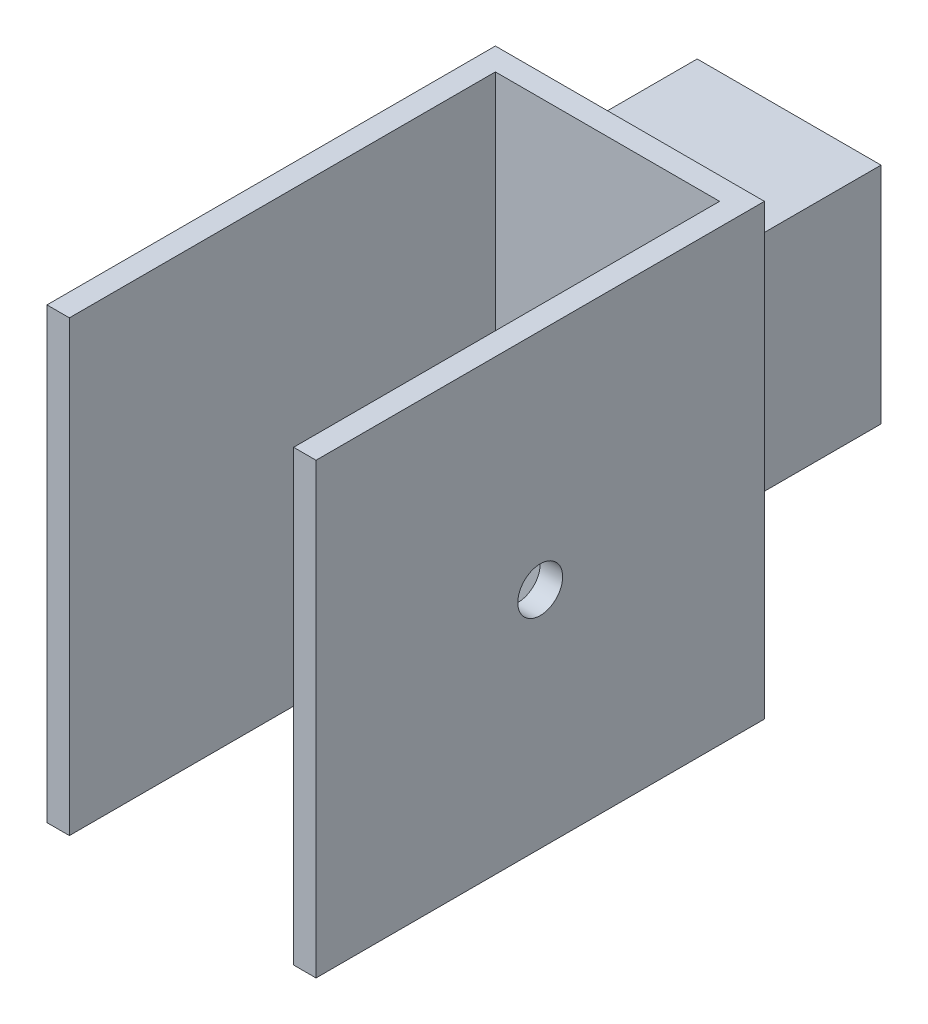
SolidWorks part; units mm, degrees
ref_plane "Piano frontale" through (0, 0, 0) normal (0, 0, 1) x (1, 0, 0)
ref_plane "Piano superiore" through (0, 0, 0) normal (0, 1, 0) x (1, 0, 0)
ref_plane "Piano destro" through (0, 0, 0) normal (1, 0, 0) x (0, 0, -1)
sketch "Schizzo1" plane through (0, 0, 0) normal (0, 0, 1) x (1, 0, 0)
  line L1 (30, -50) -> (-30, -50)
  line L2 (30, -50) -> (30, 50)
  line L3 (30, 50) -> (-30, 50)
  line L4 (-30, -50) -> (-30, 50)
  line L5 (30, -50) -> (-30, 50) construction
  line L6 (30, 50) -> (-30, -50) construction
  point P0 (0, 0)
  dimension "D1" = 60
  dimension "D2" = 100
extrude "Estrusione-Estrusione1" add sketch "Schizzo1" along normal blind 100
sketch "Schizzo2" plane through (0, 50, 0) normal (0, 1, 0) x (1, 0, 0)
  line L0 (-30, -100) -> (-30, 0) construction
  line L1 (25, -100) -> (-25, -100)
  line L2 (25, -100) -> (25, -5)
  line L3 (25, -5) -> (-25, -5)
  line L4 (-25, -100) -> (-25, -5)
  line L5 (25, -100) -> (-25, -5) construction
  line L6 (25, -5) -> (-25, -100) construction
  line L7 (30, -100) -> (30, 0) construction
  line L8 (30, -100) -> (-30, -100) construction
  line L9 (30, 0) -> (-30, 0) construction
  point P0 (0, -52.5)
  dimension "D1" = 5
  dimension "D2" = 5
  dimension "D3" = 0
  dimension "D4" = 5
extrude "Taglio-Estrusione1" cut sketch "Schizzo2" against normal through all
sketch "Schizzo3" plane through (30, 0, 0) normal (1, 0, 0) x (0, 0, -1)
  line L0 (-50, 50) -> (-50, 0)
  line L1 (-100, 50) -> (0, 50) construction
  circle A0 centre (-50, 0) radius 5
  dimension "D1" = 10
extrude "Taglio-Estrusione2" cut sketch "Schizzo3" against normal blind 21
sketch "Schizzo4" plane through (0, 0, 0) normal (0, 0, -1) x (-1, 0, 0)
  line L1 (-11, 25) -> (30, 25)
  line L2 (-11, 25) -> (-11, -25)
  line L3 (-11, -25) -> (30, -25)
  line L4 (30, 25) -> (30, -25)
  line L8 (-30, 50) -> (30, 50) construction
  line L10 (30, 50) -> (30, -50) construction
  dimension "D1" = 41
  dimension "D2" = 50
  dimension "D3" = 0
  dimension "D4" = 25
extrude "Estrusione-Estrusione2" add sketch "Schizzo4" along normal blind 45
shell "Svuota1" thickness 2
